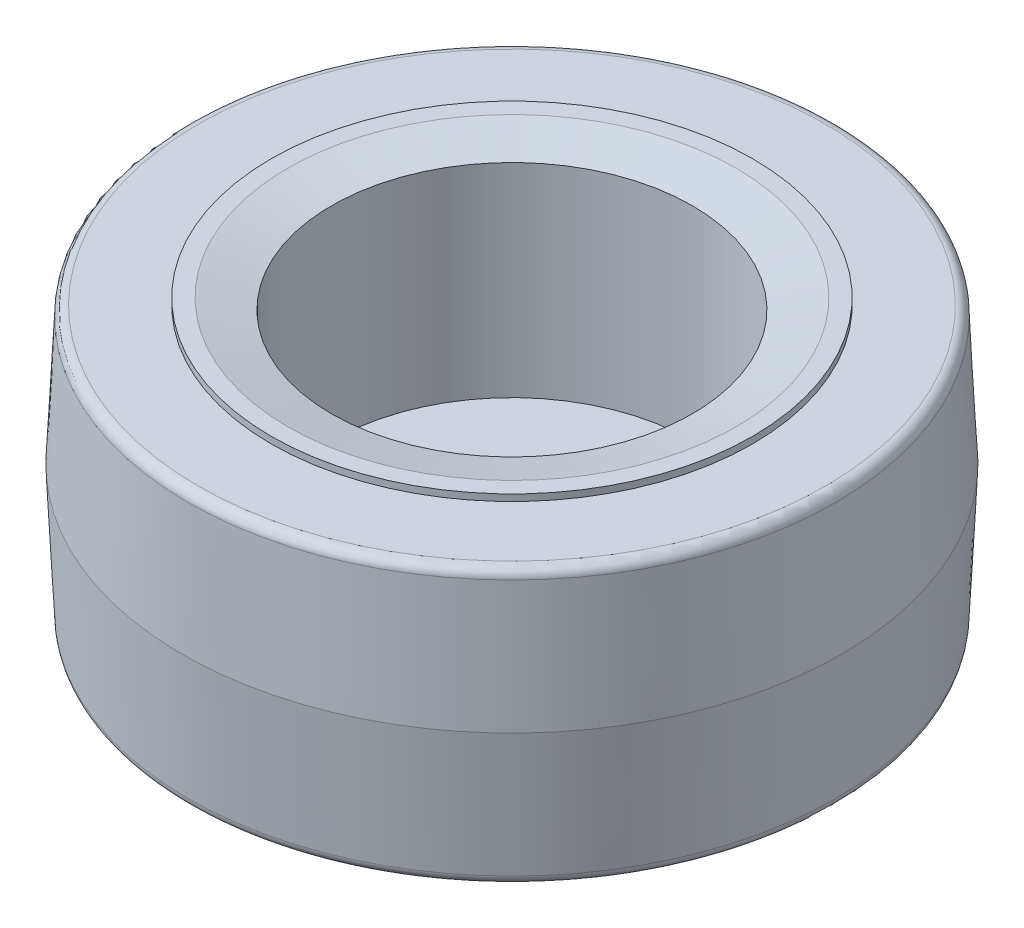
SolidWorks part; units mm, degrees
ref_plane "Front Plane" through (0, 0, 0) normal (0, 0, 1) x (1, 0, 0)
ref_plane "Top Plane" through (0, 0, 0) normal (0, 1, 0) x (1, 0, 0)
ref_plane "Right Plane" through (0, 0, 0) normal (1, 0, 0) x (0, 0, -1)
sketch "Sketch2" plane through (0, 0, 0) normal (0, 0, 1) x (1, 0, 0)
  line L0 (0, 0) -> (0, 84.4615) construction
  line L1 (6.35, -11.1125) -> (6.35, 11.1125)
  line L2 (6.35, 11.1125) -> (8.89, 11.1125)
  line L3 (12.3105, 9.9097) -> (17.272, 11.1125)
  line L4 (17.272, 11.1125) -> (18.542, 11.1125)
  line L5 (18.542, 11.1125) -> (18.542, 10.6045)
  line L6 (18.542, 10.6045) -> (24.892, 10.6045)
  line L7 (24.892, 10.6045) -> (25.4, 0)
  line L8 (25.4, 0) -> (6.35, 0) construction
  line L9 (24.892, -10.6045) -> (25.4, 0)
  line L10 (18.542, -10.6045) -> (24.892, -10.6045)
  line L11 (18.542, -11.1125) -> (18.542, -10.6045)
  line L12 (17.272, -11.1125) -> (18.542, -11.1125)
  line L13 (12.3105, -9.9097) -> (17.272, -11.1125)
  line L14 (6.35, -11.1125) -> (8.89, -11.1125)
  arc A0 (8.89, 11.1125) -> (10.3609, 10.4825) centre (8.89, 9.0805) cw
  arc A1 (10.3609, 10.4825) -> (12.3105, 9.9097) centre (11.8317, 11.8845) ccw
  arc A2 (10.3609, -10.4825) -> (12.3105, -9.9097) centre (11.8317, -11.8845) cw
  arc A3 (8.89, -11.1125) -> (10.3609, -10.4825) centre (8.89, -9.0805) ccw
  dimension "D6" = 2.032
  dimension "D1" = 22.225
  dimension "D2" = 12.7
  dimension "D3" = 6.35
  dimension "D4" = 1.27
  dimension "D5" = 2.54
  dimension "D7" = 0.508
  dimension "D8" = 50.8
  dimension "D9" = 0.508
revolve "Revolve1" add sketch "Sketch2" angle 360 about L0
fillet "Fillet1" radius 0.762 2 edges at (0, -10.6045, -24.892) (0, 10.6045, -24.892)
sketch "Sketch3" plane through (0, 11.1125, 0) normal (0, 1, 0) x (-1, 0, 0)
  circle A0 centre (0, 0) radius 13.9002
  dimension "D1" = 27.8003
extrude "Cut-Extrude1" cut sketch "Sketch3" against normal blind 16.51
